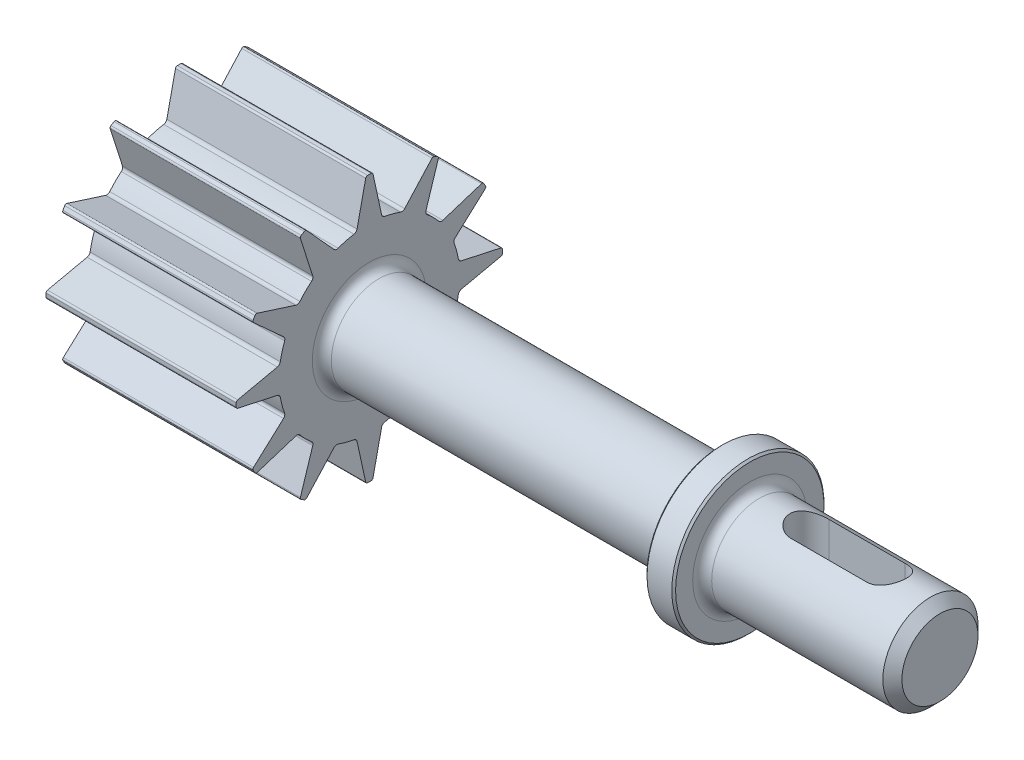
SolidWorks part; units mm, degrees
ref_plane "Front Plane" through (0, 0, 0) normal (0, 0, 1) x (1, 0, 0)
ref_plane "Top Plane" through (0, 0, 0) normal (0, 1, 0) x (1, 0, 0)
ref_plane "Right Plane" through (0, 0, 0) normal (1, 0, 0) x (0, 0, -1)
sketch "Sketch1" plane through (0, 0, 0) normal (1, 0, 0) x (0, 0, -1)
  line L0 (0, 0) -> (0, 7) construction
  line L1 (-0.6459, 4.8354) -> (-0.1918, 6.9206)
  line L2 (0.6459, 4.8354) -> (0.1918, 6.9206)
  arc A0 (-0.8073, 4.6809) -> (0.8073, 4.6809) centre (0, 0) ccw
  arc A1 (0.0955, 6.9993) -> (-0.0955, 6.9993) centre (0, 0) ccw
  arc A2 (0.1918, 6.9206) -> (0.0955, 6.9993) centre (0.0941, 6.8994) ccw
  arc A3 (-0.1918, 6.9206) -> (-0.0955, 6.9993) centre (-0.0941, 6.8994) cw
  arc A4 (0.6459, 4.8354) -> (0.8073, 4.6809) centre (0.8413, 4.878) ccw
  arc A5 (-0.6459, 4.8354) -> (-0.8073, 4.6809) centre (-0.8413, 4.878) cw
  point P9 (0.175, 6.9978)
  point P12 (-0.175, 6.9978)
  point P15 (0.675, 4.7018)
  point P18 (-0.675, 4.7018)
  dimension "D1" = 9.5
  dimension "D2" = 14
  dimension "D5" = 0.1
  dimension "D6" = 0.2
  dimension "D3" = 0.175
  dimension "D4" = 0.675
extrude "Boss-Extrude1" add sketch "Sketch1" along normal blind 10
pattern_circular "CirPattern1" count 12 over 360 about axis through (0, 0, 0) along (1, 0, 0) of "Boss-Extrude1"
sketch "Sketch2" plane through (10, 0, 0) normal (1, 0, 0) x (0, 0, -1)
  circle A0 centre (0, 0) radius 2.5
  dimension "D1" = 5
extrude "Boss-Extrude2" add sketch "Sketch2" along normal blind 30
sketch "Sketch6" plane through (0, 0, 0) normal (0, 1, 0) x (1, 0, 0)
  line L0 (0, 0) -> (40, 0) construction
  line L1 (40, -2.5) -> (40, 2.5) construction
  line L3 (28.5, 4) -> (30, 4)
  line L4 (28.5, 4) -> (28.5, 2.5)
  line L5 (28.5, 2.5) -> (30, 2.5)
  line L6 (30, 4) -> (30, 2.5)
  line L7 (28.5, 4) -> (30, 2.5) construction
  line L8 (28.5, 2.5) -> (30, 4) construction
  point P5 (29.25, 3.25)
  dimension "D1" = 1.5
  dimension "D2" = 1.5
  dimension "D3" = 2.5
  dimension "D4" = 10
revolve "Revolve1" add sketch "Sketch6" angle 360 about L0
ref_plane "Plane1" through (0, 2.5, 0) normal (0, 1, 0) x (1, 0, 0)
sketch "Sketch8" plane through (0, 2.5, 0) normal (0, 1, 0) x (1, 0, 0)
  line L0 (37, 0.1557) -> (33, 0.1557) construction
  line L1 (37, -0.8443) -> (33, -0.8443)
  line L2 (37, 1.1557) -> (33, 1.1557)
  line L4 (40, -2.5) -> (40, 2.5) construction
  arc A0 (37, -0.8443) -> (37, 1.1557) centre (37, 0.1557) ccw
  arc A1 (33, 1.1557) -> (33, -0.8443) centre (33, 0.1557) ccw
  point P2 (35, 0.1557)
  dimension "D1" = 1
  dimension "D2" = 4
  dimension "D3" = 5
extrude "Cut-Extrude1" cut sketch "Sketch8" against normal blind 4
chamfer "Chamfer2" distance 0.5 angle 45 1 edges at (40, 0, -2.5)
fillet "Fillet1" radius 0.5 2 edges at (28.5, 0, -2.5) (30, 0, 2.5)
chamfer "Chamfer3" distance 0.1 angle 45 2 edges at (28.5, 0, 4) (30, 0, 4)
fillet "Fillet2" radius 0.5 1 edges at (10, 0, -2.5)
sketch "Sketch9" plane through (0, 0, 0) normal (-1, 0, 0) x (0, 0, 1)
  circle A0 centre (0, 0) radius 3.25
  dimension "D1" = 6.5
extrude "Cut-Extrude2" cut sketch "Sketch9" against normal blind 1
